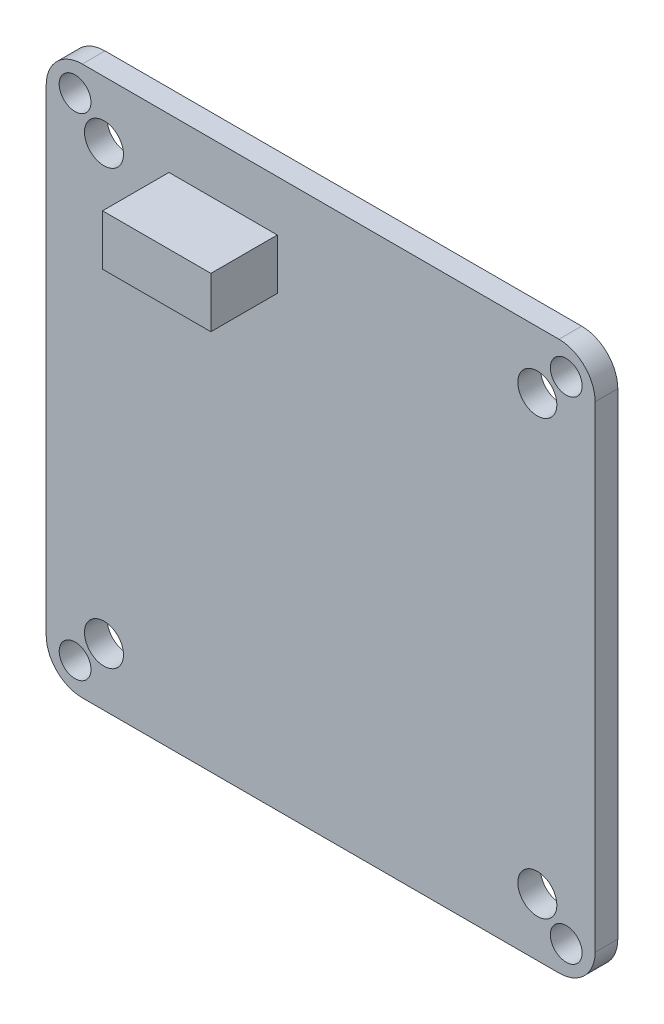
SolidWorks part; units mm, degrees
ref_plane "Front" through (0, 0, 0) normal (0, 0, 1) x (1, 0, 0)
ref_plane "Top" through (0, 0, 0) normal (0, 1, 0) x (1, 0, 0)
ref_plane "Right" through (0, 0, 0) normal (1, 0, 0) x (0, 0, -1)
sketch "Sketch1" plane through (0, 0, 0) normal (0, 0, 1) x (1, 0, 0)
  line L1 (-19, -19) -> (19, -19)
  line L2 (-19, -19) -> (-19, 19)
  line L3 (-19, 19) -> (19, 19)
  line L4 (19, -19) -> (19, 19)
  line L5 (-19, -19) -> (19, 19) construction
  line L6 (-19, 19) -> (19, -19) construction
  point P0 (0, 0)
  dimension "D1" = 38
extrude "Boss-Extrude1" add sketch "Sketch1" along normal blind 1.57
fillet "Fillet1" radius 2.5 4 edges at (-19, -19, 0.785) (19, -19, 0.785) (19, 19, 0.785) (-19, 19, 0.785)
hole_wizard "M2 Clearance Hole1" positions "Sketch2" profile "Sketch3" hole size "M2" standard "ANSI Metric" end condition through all
sketch "Sketch2" plane through (0, 0, 1.57) normal (0, 0, 1) x (1, 0, 0)
  line L2 (-17, 17) -> (17, 17)
  line L3 (-17, 17) -> (-17, -17)
  line L4 (-17, -17) -> (17, -17)
  line L5 (17, 17) -> (17, -17)
  line L6 (-17, 0) -> (17, 0) construction
  point P0 (-17, 17)
  point P124 (17, -17)
  point P201 (-17, -17)
  point P202 (17, 17)
  point P212 (0, 0)
  dimension "D1" = 34
sketch "Sketch3" plane through (-17, 17, 1.57) normal (1, 0, 0) x (0, -1, 0)
  line L0 (0, 0) -> (0, 1.57)
  line L1 (0, 1.57) -> (1.1, 1.57)
  line L2 (1.1, 1.57) -> (1.1, 0)
  line L5 (1.1, 0) -> (0, 0)
  line L11 (0, -6.35) -> (0, 107.95) construction
  dimension "Thru Hole Dia." = 2.2
  dimension "Thru Hole Depth" = 1.57
hole_wizard "M2.5 Clearance Hole1" positions "Sketch4" profile "Sketch5" hole size "M2.5" standard "ANSI Metric" end condition through all
sketch "Sketch4" plane through (0, 0, 1.57) normal (0, 0, 1) x (1, 0, 0)
  line L1 (-15, 15) -> (15, 15)
  line L2 (-15, 15) -> (-15, -15)
  line L3 (-15, -15) -> (15, -15)
  line L4 (15, 15) -> (15, -15)
  line L5 (-15, 0) -> (15, 0) construction
  point P0 (-15, 15)
  point P4 (15, -15)
  point P97 (-15, -15)
  point P98 (15, 15)
  point P106 (0, 0)
  dimension "D1" = 30
sketch "Sketch5" plane through (-15, 15, 1.57) normal (1, 0, 0) x (0, -1, 0)
  line L0 (0, 0) -> (0, 1.57)
  line L1 (0, 1.57) -> (1.35, 1.57)
  line L2 (1.35, 1.57) -> (1.35, 0)
  line L5 (1.35, 0) -> (0, 0)
  line L11 (0, -6.35) -> (0, 107.95) construction
  dimension "Thru Hole Dia." = 2.7
  dimension "Thru Hole Depth" = 1.57
sketch "Sketch6" plane through (0, 0, 1.57) normal (0, 0, 1) x (1, 0, 0)
  line L0 (-19, 16.5) -> (-19, -16.5) construction
  line L1 (-10.5, 15.5) -> (-3, 15.5)
  line L2 (-10.5, 15.5) -> (-10.5, 12)
  line L3 (-10.5, 12) -> (-3, 12)
  line L4 (-3, 15.5) -> (-3, 12)
  line L5 (16.5, 19) -> (-16.5, 19) construction
  dimension "D1" = 7.5
  dimension "D2" = 3.5
  dimension "D3" = 8.5
  dimension "D4" = 3.5
extrude "Boss-Extrude2" add sketch "Sketch6" along normal blind 4.6 separate body
